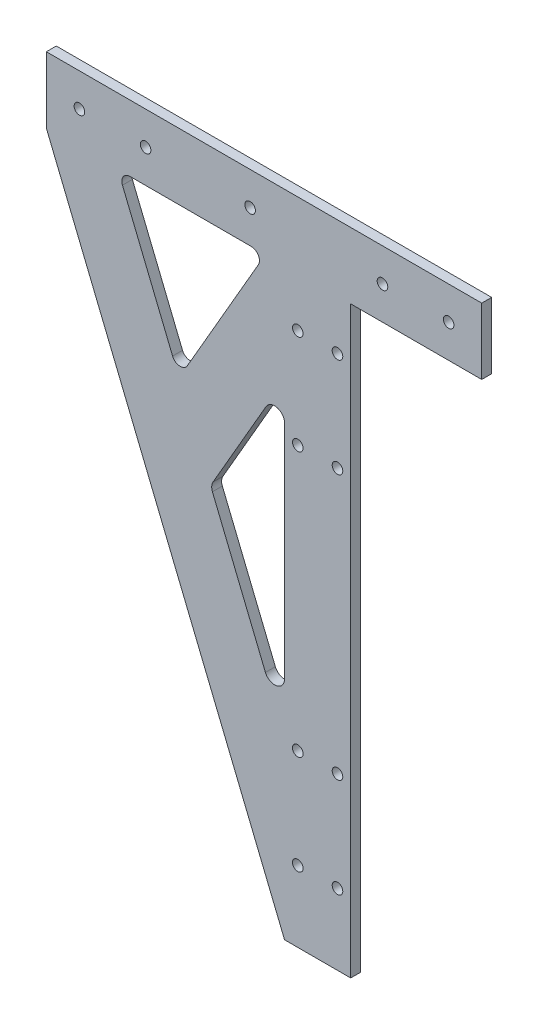
SolidWorks part; units mm, degrees
material "Thornel Mat VMA"
ref_plane "Front Plane" through (0, 0, 0) normal (0, 0, 1) x (1, 0, 0)
ref_plane "Top Plane" through (0, 0, 0) normal (0, 1, 0) x (1, 0, 0)
ref_plane "Right Plane" through (0, 0, 0) normal (1, 0, 0) x (0, 0, -1)
sketch "Sketch1" plane through (0, 0, 0) normal (0, 0, 1) x (1, 0, 0)
  line L1 (-234.4582, 0) -> (-162.4582, -176.4706)
  line L2 (-162.4582, -470) -> (-162.4582, 0) construction
  line L4 (-142.4582, -470) -> (-142.4582, 0) construction
  line L6 (-234.4582, 20) -> (284.7418, 20) construction
  line L7 (-102.8636, 20) -> (-234.4582, 20)
  line L8 (-234.4582, 10) -> (-102.8582, 10) construction
  line L9 (-234.4582, 20) -> (-234.4582, 0) construction
  line L10 (-102.8636, 20) -> (-102.8582, 20)
  line L11 (-102.8582, 20) -> (-102.8582, 0)
  line L12 (-102.8582, 0) -> (-142.4582, 0)
  line L13 (-102.8582, 0) -> (-102.8582, 20) construction
  line L15 (-182.8582, 0) -> (-162.4582, -50) construction
  line L17 (-234.4582, 0) -> (-162.4582, 0) construction
  line L18 (-209.1527, 0) -> (-172.5442, 0)
  line L19 (-170.3879, -3.7347) -> (-191.8381, -40.8875)
  line L21 (-196.2997, -40.5832) -> (-211.458, -3.4304)
  line L25 (-234.4582, 20) -> (-234.4582, 0)
  line L26 (-162.4582, -176.4706) -> (-142.4582, -176.4706)
  line L27 (-162.4582, -41.1962) -> (-162.4582, -108.2336)
  line L28 (-162.4582, -270) -> (-162.4582, 0) construction
  line L29 (-168.2359, -109.3669) -> (-184.2619, -70.0874)
  line L30 (-184.0823, -67.4541) -> (-168.0563, -39.6962)
  line L31 (-142.4582, -176.4706) -> (-142.4582, 0)
  circle A0 centre (-112.8582, 10) radius 1.6 construction
  circle A1 centre (-132.8582, 10) radius 1.6 construction
  circle A2 centre (-172.8582, 10) radius 1.6 construction
  circle A3 centre (-112.8582, 10) radius 1.6
  circle A4 centre (-132.8582, 10) radius 1.6
  circle A5 centre (-172.8582, 10) radius 1.6
  circle A6 centre (-146.4582, -45) radius 1.6 construction
  circle A7 centre (-158.4582, -45) radius 1.6 construction
  circle A8 centre (-146.4582, -15) radius 1.6 construction
  circle A9 centre (-158.4582, -15) radius 1.6 construction
  circle A10 centre (-146.4582, -45) radius 1.6
  circle A11 centre (-158.4582, -45) radius 1.6
  circle A12 centre (-146.4582, -15) radius 1.6
  circle A13 centre (-158.4582, -15) radius 1.6
  circle A18 centre (-224.4582, 10) radius 1.6
  circle A19 centre (-204.4582, 10) radius 1.6
  arc A26 (-170.3879, -3.7347) -> (-172.5442, 0) centre (-172.5442, -2.4898) ccw
  arc A27 (-191.8381, -40.8875) -> (-196.2997, -40.5832) centre (-193.9943, -39.6426) cw
  arc A28 (-211.458, -3.4304) -> (-209.1527, 0) centre (-209.1527, -2.4898) cw
  circle A29 centre (-158.4582, -125) radius 1.6
  circle A30 centre (-146.4582, -125) radius 1.6
  circle A31 centre (-158.4582, -155) radius 1.6
  circle A32 centre (-146.4582, -155) radius 1.6
  arc A33 (-162.4582, -108.2336) -> (-168.2359, -109.3669) centre (-165.4582, -108.2336) cw
  arc A34 (-162.4582, -41.1962) -> (-168.0563, -39.6962) centre (-165.4582, -41.1962) ccw
  arc A35 (-184.2619, -70.0874) -> (-184.0823, -67.4541) centre (-181.4842, -68.9541) cw
  point P70 (-102.5734, 20)
  point P73 (-162.4582, -123.528)
  point P74 (-162.4582, -123.528)
  point P77 (-162.4582, -30)
  point P80 (-102.8636, 20)
  point P90 (-194.3795, -45.2894)
  point P93 (-212.8576, 0)
  dimension "D1" = 3.2
  dimension "D2" = 10
  dimension "D3" = 20
  dimension "D8" = 3
  dimension "D4" = 20
  dimension "D5" = 20
  dimension "D6" = 30
  dimension "D7" = 30
  dimension "D9" = 2
extrude "Extrude1" add sketch "Sketch1" along normal blind 3
